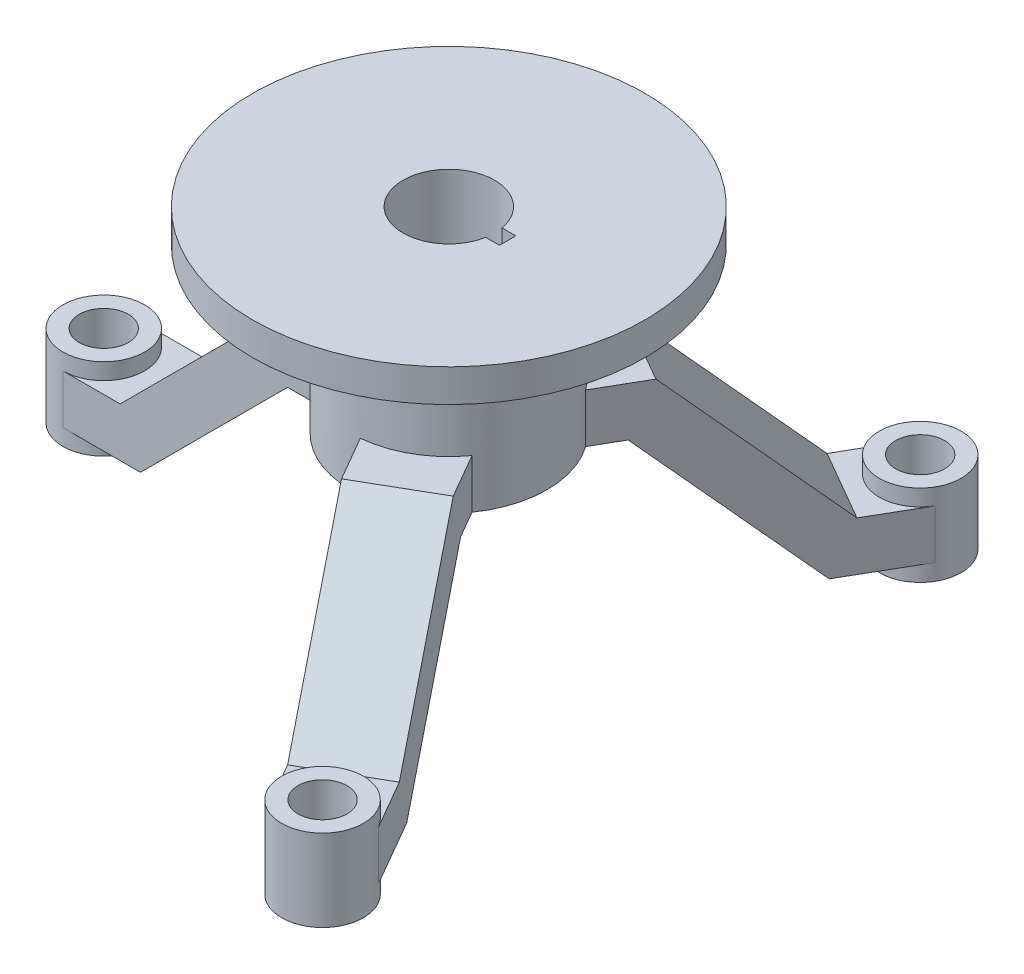
SolidWorks part; units mm, degrees
material "AISI 304"
ref_plane "Front Plane" through (0, 0, 0) normal (0, 0, 1) x (1, 0, 0)
ref_plane "Top Plane" through (0, 0, 0) normal (0, 1, 0) x (1, 0, 0)
ref_plane "Right Plane" through (0, 0, 0) normal (1, 0, 0) x (0, 0, -1)
sketch "Sketch1" plane through (0, 0, 0) normal (0, 1, 0) x (1, 0, 0)
  circle A0 centre (0, 0) radius 120
  dimension "D1" = 240
extrude "Boss-Extrude1" add sketch "Sketch1" along normal blind 20
sketch "Sketch2" plane through (0, 0, 0) normal (0, -1, 0) x (1, 0, 0)
  circle A0 centre (0, 0) radius 60
  dimension "D1" = 120
extrude "Boss-Extrude2" add sketch "Sketch2" along normal blind 100
sketch "Sketch3" plane through (0, 20, 0) normal (0, 1, 0) x (1, 0, 0)
  line L0 (0, 0) -> (88.6751, 0) construction
  line L2 (27.55, 5) -> (36, 5)
  line L4 (27.55, -5) -> (36, -5)
  line L5 (36, 5) -> (36, -5)
  arc A0 (27.55, 5) -> (27.55, -5) centre (0, 0) ccw
  dimension "D1" = 28
  dimension "D2" = 10
  dimension "D3" = 36
extrude "Cut-Extrude1" cut sketch "Sketch3" against normal through all
sketch "Sketch4" plane through (0, 0, 0) normal (0, 0, 1) x (1, 0, 0)
  line L0 (-45.5827, -70) -> (-86, -70)
  line L1 (-86, -70) -> (-176, -160)
  line L2 (-176, -160) -> (-211, -160)
  line L3 (-211, -160) -> (-211, -190)
  line L4 (-211, -190) -> (-163.5736, -190)
  line L5 (-163.5736, -190) -> (-73.5736, -100)
  line L6 (-73.5736, -100) -> (-45.5827, -100)
  line L7 (-60, -100) -> (60, -100) construction
  line L8 (-45.5827, -70) -> (-45.5827, -100)
  dimension "D1" = 30
  dimension "D2" = 30
  dimension "D3" = 30
  dimension "D4" = 86
  dimension "D5" = 45
  dimension "D6" = 35
  dimension "D7" = 120
extrude "Boss-Extrude3" add sketch "Sketch4" along normal mid plane 50
sketch "Sketch5" plane through (0, -160, 0) normal (0, 1, 0) x (1, 0, 0)
  line L0 (-211, -25) -> (-211, 25) construction
  circle A0 centre (-211, 0) radius 25
  dimension "D1" = 50
extrude "Boss-Extrude4" add sketch "Sketch5" along normal blind 10 and the other way blind 40
sketch "Sketch6" plane through (0, -150, 0) normal (0, 1, 0) x (1, 0, 0)
  circle A0 centre (-211, 0) radius 15
  dimension "D1" = 30
extrude "Cut-Extrude2" cut sketch "Sketch6" against normal through all
pattern_circular "CirPattern1" count 3 over 360 about axis through (0, 0, 0) along (0, 1, 0) of "Boss-Extrude4", "Cut-Extrude2", "Boss-Extrude3"
fillet "Fillet2" radius 10 1 edges at (0, 0, -60)
